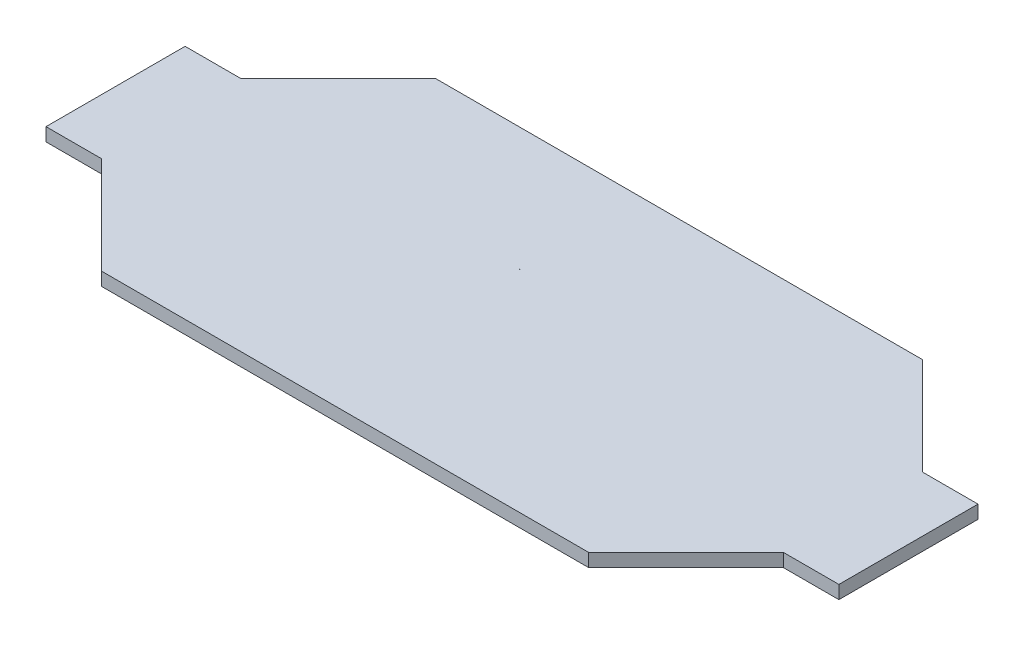
SolidWorks part; units mm, degrees
material "Pine"
ref_plane "Front Plane" through (0, 0, 0) normal (0, 0, 1) x (1, 0, 0)
ref_plane "Top Plane" through (0, 0, 0) normal (0, 1, 0) x (1, 0, 0)
ref_plane "Right Plane" through (0, 0, 0) normal (1, 0, 0) x (0, 0, -1)
sketch "Sketch1" plane through (0, 0, 0) normal (0, 1, 0) x (1, 0, 0)
  line L0 (-75, 60) -> (100, 60)
  line L1 (100, 60) -> (135, 25)
  line L2 (135, 25) -> (155, 25)
  line L3 (155, 25) -> (155, -25)
  line L4 (155, -25) -> (135, -25)
  line L5 (135, -25) -> (100, -60)
  line L6 (100, -60) -> (-75, -60)
  line L7 (-75, -60) -> (-110, -25)
  line L8 (-110, -25) -> (-130, -25)
  line L9 (-130, -25) -> (-130, 25)
  line L10 (-130, 25) -> (-110, 25)
  line L11 (-110, 25) -> (-75, 60)
  line L12 (-55, 0) -> (55, 0) construction
  line L13 (-42.9998, 14.9814) -> (-42.9998, 2.9814)
  line L14 (-42.325, 15.7594) -> (-35.0369, 4.0877)
  line L16 (-35, 3) -> (-41, 3)
  line L17 (-69.6792, 10) -> (88.0424, 10) construction
  line L18 (0, -55) -> (0, 55) construction
  line L19 (-23.6515, 14.1748) -> (-14.1337, -1.0676) construction
  line L20 (0.1562, 3.1942) -> (0.1562, 16.2943)
  line L21 (-0.8262, 3.1942) -> (-5.7582, 13.8399)
  line L22 (-6.0961, 15.8087) -> (-0.0961, 15.8087)
  line L23 (-42.2885, 15.8087) -> (-40.1061, 15.8087) construction
  line L24 (-25.855, 3) -> (-30.8412, 3) construction
  line L25 (-148.3275, 0) -> (158.1796, 0) construction
  arc A0 (-42.9998, 14.9814) -> (-42.325, 15.7594) centre (-42.0149, 14.8087) cw
  arc A1 (-42.9998, 2.9814) -> (-41, 3) centre (-41.9998, 2.9814) ccw
  arc A2 (-35.0369, 4.0877) -> (-35, 3) centre (-35.857, 3.5154) cw
  arc A3 (0.1562, 3.1942) -> (-0.8262, 3.1942) centre (-0.335, 3.7183) cw
  arc A4 (0.1562, 16.2943) -> (-0.0961, 15.8087) centre (-0.4373, 16.2943) ccw
  arc A5 (-5.7582, 13.8399) -> (-6.0961, 15.8087) centre (-5.9761, 14.8159) cw
  point P36 (-0.335, 3)
  dimension "D8" = 1
  dimension "D9" = 1
  dimension "D10" = 1
  dimension "D22" = 1
  dimension "D20" = 15
  dimension "D17" = 10
  dimension "D3" = 50
  dimension "D4" = 175
  dimension "D5" = 25
  dimension "D6" = 20
  dimension "D7" = 0
  dimension "D11" = 3
  dimension "D12" = 130
  dimension "D13" = 120
  dimension "D14" = 60
  dimension "D15" = 6
  dimension "D18" = 35
  dimension "D21" = 12
  dimension "D24" = 6
  dimension "D25" = 3
  dimension "D26" = 15
extrude "Boss-Extrude2" add sketch "Sketch1" along normal blind 4.75 contours A5 L21 A3 L20 A4 L22 | A2 L14 A0 L13 A1 L16 | L11 L10 L9 L8 L7 L6 L5 L4 L3 L2 L1 L0 L14 A2 L16 A1 L13 A0 L21 A5 L22 A4 L20 A3
